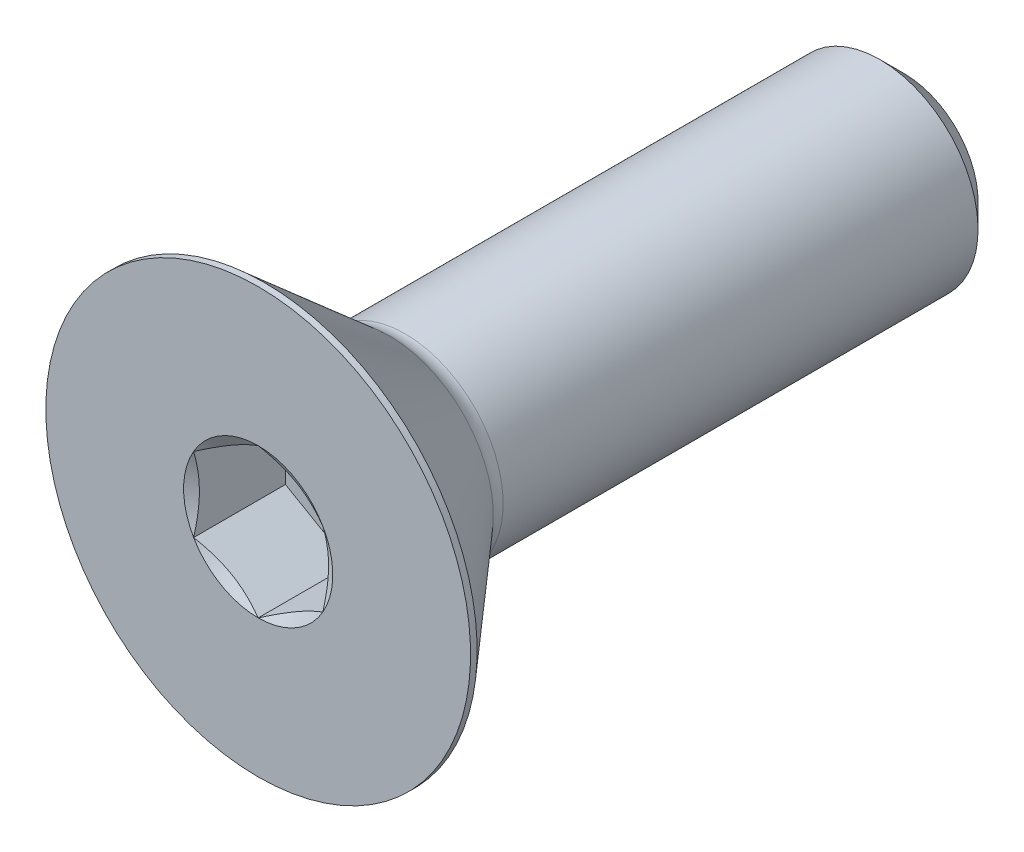
SolidWorks part; units mm, degrees
material "Plain Carbon Steel"
ref_plane "Front" through (0, 0, 0) normal (0, 0, 1) x (1, 0, 0)
ref_plane "Top" through (0, 0, 0) normal (0, 1, 0) x (1, 0, 0)
ref_plane "Right" through (0, 0, 0) normal (1, 0, 0) x (0, 0, -1)
sketch "Sketch1" plane through (0, 0, 0) normal (1, 0, 0) x (0, 0, -1)
  line L0 (0, 5.2197) -> (0.1613, 5.2197) construction
  line L1 (0.1613, 5.2197) -> (3.2258, 2.5558) construction
  line L2 (0, 2.413) -> (15.875, 2.413)
  line L3 (15.875, 2.413) -> (15.875, 0)
  line L4 (15.875, 0) -> (0, 0)
  line L5 (0, 0) -> (0, 5.2197) construction
  line L6 (0, 5.2197) -> (0, -5.2197) construction
  line L7 (15.875, 2.413) -> (15.875, -2.413) construction
  line L8 (0, -5.2197) -> (0.1613, -5.2197) construction
  line L9 (0.1613, -5.2197) -> (3.2258, -2.5558) construction
  line L11 (0, 2.413) -> (0, 0)
  line L12 (3.6076, 2.413) -> (3.6076, 0) construction
  line L13 (-9.525, 0) -> (-9.525, 2.413) construction
  arc A1 (3.2258, 2.5558) -> (3.6076, 2.413) centre (3.6076, 2.995) ccw construction
  dimension "D1" = 0.1613
  dimension "Min Thread" = 25.4
revolve "Revolve1" add sketch "Sketch1" angle 360 mid plane about L4
ref_plane "Plane2" through (0, 0, 9.525) normal (0, 0, 1) x (1, 0, 0)
chamfer "Chamfer1" distance 0.5953 angle 45 1 edges at (0, 2.413, -15.875)
sketch "Sketch7" plane through (0, 0, 0) normal (1, 0, 0) x (0, 0, -1)
  line L0 (0, 5.2197) -> (0.1613, 5.2197) construction
  line L1 (0.1613, 5.2197) -> (3.2258, 2.5558) construction
  line L2 (0, 5.2197) -> (0.1613, 5.2197)
  line L3 (0.1613, 5.2197) -> (3.2258, 2.5558)
  line L4 (3.6076, 2.413) -> (3.6076, 0) construction
  line L5 (3.6076, 2.413) -> (3.6076, 0)
  line L7 (0, 0) -> (0, 5.2197) construction
  line L8 (0, 0) -> (0, 5.2197)
  line L9 (0, 0) -> (3.6076, 0)
  line L10 (5.7417, 0) -> (-5.7417, 0) construction
  arc A0 (3.2258, 2.5558) -> (3.6076, 2.413) centre (3.6076, 2.995) ccw construction
  arc A1 (3.2258, 2.5558) -> (3.6076, 2.413) centre (3.6076, 2.995) ccw
revolve "Revolve2" add sketch "Sketch7" angle 360 mid plane about L9
ref_plane "Plane1" through (0, 0, -3.6076) normal (0, 0, 1) x (1, 0, 0)
sketch "Sketch5" plane through (0, 0, 0) normal (0, 0, 1) x (1, 0, 0)
  line L0 (0, 0) -> (-1.8331, 0) construction
  line L1 (0, 0) -> (-2.7496, 1.5875) construction
  line L2 (0, 0) -> (-2.7496, -1.5875) construction
  line L6 (0, 1.8331) -> (0, 1.5119) construction
  line L7 (0, 1.5119) -> (0, 1.1906) construction
  line L9 (0, 1.8331) -> (-1.5875, 0.9165)
  line L10 (-1.5875, 0.9165) -> (-1.5875, -0.9165)
  line L11 (-1.5875, -0.9165) -> (0, -1.8331)
  line L12 (0, -1.8331) -> (1.5875, -0.9165)
  line L13 (1.5875, -0.9165) -> (1.5875, 0.9165)
  line L14 (1.5875, 0.9165) -> (0, 1.8331)
  circle A0 centre (0, 0) radius 1.8331 construction
  circle A1 centre (0, 0) radius 1.5119 construction
  circle A2 centre (0, 0) radius 1.1906 construction
  circle A3 centre (0, 0) radius 1.5875 construction
  dimension "D3" = 2.3813
  dimension "D4" = 30
  dimension "D5" = 30
extrude "Cut-Extrude2" cut sketch "Sketch5" against normal blind 2.2581
sketch "Sketch6" plane through (0, 0, 0) normal (0, 0, 1) x (1, 0, 0)
  circle A0 centre (0, 0) radius 1.8331
extrude "Cut-Extrude3" cut sketch "Sketch6" against normal blind 2.2581 draft 60
sketch "Sketch9" [suppressed] plane through (0, 0, -3.6076) normal (0, 0, 1) x (1, 0, 0)
  circle A1 centre (0, 0) radius 2.413
  circle A2 centre (0, 0) radius 2.413
  point P0 (0, 2.413)
  dimension "D1" = 0
extrude "Boss-Extrude2" [suppressed] add sketch "Sketch9" against normal up to surface (15.4424 mm away)
move or copy body "Body-Move/Copy1" [suppressed] bodies to move or copy 113
equation "\"D1@Cut-Extrude2\" = \"Head Ht@Sketch1\" * .7"
equation "\"D1@Sketch1\" = \"Head Ht@Sketch1\" * .05"
equation "\"D1@Cut-Extrude3\" = \"D1@Cut-Extrude2\""
equation "\"D3@Sketch5\" = \"Hex@Sketch5\" * .75"
